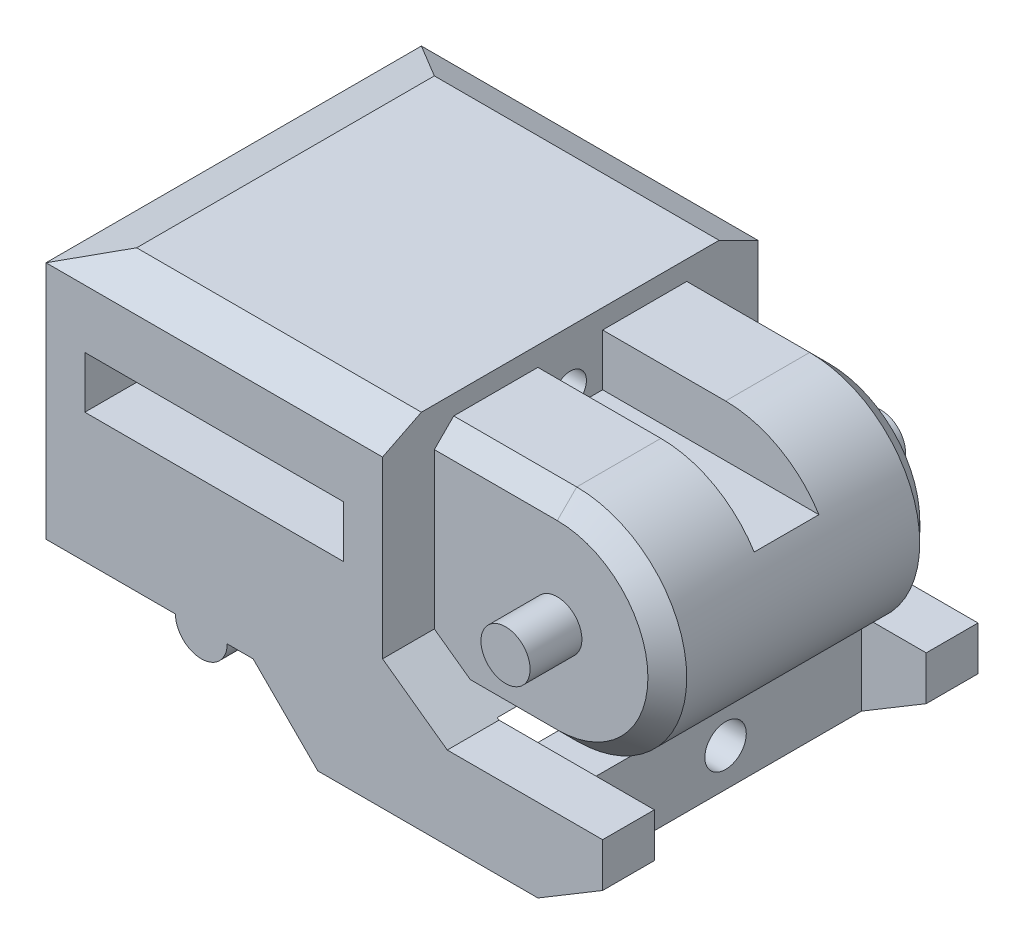
SolidWorks part; units mm, degrees
ref_plane "Front Plane" through (0, 0, 0) normal (0, 0, 1) x (1, 0, 0)
ref_plane "Top Plane" through (0, 0, 0) normal (0, 1, 0) x (1, 0, 0)
ref_plane "Right Plane" through (0, 0, 0) normal (1, 0, 0) x (0, 0, -1)
sketch "Sketch1" plane through (0, 0, 0) normal (0, 1, 0) x (1, 0, 0)
  line L0 (-8.5, 14.5) -> (-8.5, -14.5)
  line L1 (-8.5, -14.5) -> (35.5, -14.5)
  line L3 (-8.5, 14.5) -> (35.5, 14.5)
  line L4 (35.5, -14.5) -> (35.5, 14.5)
  line L5 (-8.5, -3.4718) -> (35.5, 14.5) construction
  line L7 (17.5, 14.5) -> (17.5, -14.5)
  line L10 (17.5, 10.5) -> (35.5, 10.5)
  line L11 (17.5, -10.5) -> (35.5, -10.5)
  line L12 (-8.5, 5.5141) -> (35.5, -14.5) construction
  point P0 (0, 0)
  dimension "D1" = 29
  dimension "D2" = 44
  dimension "D4" = 18
  dimension "D7" = 4
  dimension "D8" = 4
extrude "Boss-Extrude1" add sketch "Sketch1" along normal blind 20 contours L7 L3 L0 L1 | L7 L11 L4 L10
sketch "Sketch3" plane through (0, 0, 14.5) normal (0, 0, 1) x (1, 0, 0)
  line L0 (-8.5, 20) -> (-8.5, 18.5)
  line L1 (-8.5, 20) -> (-8.5, 0) construction
  line L2 (-8.5, 18.5) -> (-4.5, 20)
  line L3 (-4.5, 20) -> (-8.5, 20)
  dimension "D1" = 1.5
  dimension "D2" = 4
extrude "Cut-Extrude3" cut sketch "Sketch3" against normal through all
sketch "Sketch4" plane through (17.5, 0, 0) normal (1, 0, 0) x (0, 0, -1)
  line L0 (-14.5, 20) -> (-14.5, 18.5)
  line L1 (-14.5, 20) -> (-14.5, 0) construction
  line L2 (-14.5, 18.5) -> (-11.5, 20)
  line L3 (14.5, 20) -> (10.5, 20) construction
  line L4 (-11.5, 20) -> (-14.5, 20)
  line L5 (14.5, 20) -> (11.5, 20)
  line L6 (11.5, 20) -> (14.5, 18.5)
  line L7 (14.5, 20) -> (14.5, 0) construction
  line L8 (14.5, 18.5) -> (14.5, 20)
  dimension "D1" = 3
  dimension "D2" = 1.5
  dimension "D3" = 1.5
  dimension "D4" = 3
extrude "Cut-Extrude4" cut sketch "Sketch4" against normal through all
sketch "Sketch6" plane through (0, 0, 0) normal (0, -1, 0) x (1, 0, 0)
  line L0 (-8.5, -14.5) -> (17.5, -14.5) construction
  line L1 (-5.5, 8.5) -> (14.5, 8.5)
  line L2 (-5.5, 8.5) -> (-5.5, -8.5)
  line L3 (-5.5, -8.5) -> (14.5, -8.5)
  line L4 (14.5, 8.5) -> (14.5, -8.5)
  line L5 (-8.5, -14.5) -> (-8.5, 14.5) construction
  line L6 (-8.5, 14.5) -> (17.5, 14.5) construction
  line L7 (17.5, -14.5) -> (17.5, -10.5) construction
  dimension "D1" = 6
  dimension "D2" = 3
  dimension "D3" = 6
  dimension "D4" = 3
extrude "Cut-Extrude5" cut sketch "Sketch6" against normal blind 17
sketch "Sketch9" plane through (-8.5, 0, 0) normal (-1, 0, 0) x (0, 0, 1)
  line L0 (-14.5, 18.5) -> (-14.5, 0) construction
  line L1 (-8.5, 17) -> (8.5, 17)
  line L2 (-8.5, 17) -> (-8.5, 13)
  line L3 (-8.5, 13) -> (8.5, 13)
  line L4 (8.5, 17) -> (8.5, 13)
  line L5 (14.5, 18.5) -> (14.5, 0) construction
  line L6 (-14.5, 18.5) -> (14.5, 18.5) construction
  dimension "D1" = 6
  dimension "D2" = 6
  dimension "D3" = 1.5
  dimension "D4" = 4
extrude "Cut-Extrude7" cut sketch "Sketch9" against normal blind 4
sketch "Sketch10" plane through (0, 0, 14.5) normal (0, 0, 1) x (1, 0, 0)
  line L0 (-8.5, 18.5) -> (-8.5, 0) construction
  line L1 (-5.5, 14) -> (14.5, 14)
  line L2 (-5.5, 14) -> (-5.5, 10)
  line L3 (-5.5, 10) -> (14.5, 10)
  line L4 (14.5, 14) -> (14.5, 10)
  line L5 (17.5, 18.5) -> (17.5, 0) construction
  line L6 (-4.5, 20) -> (17.5, 20) construction
  dimension "D1" = 3
  dimension "D2" = 3
  dimension "D3" = 4
  dimension "D4" = 6
extrude "Cut-Extrude8" cut sketch "Sketch10" against normal through all
sketch "Sketch12" plane through (0, 0, 14.5) normal (0, 0, 1) x (1, 0, 0)
  line L0 (22.5, 1.4) -> (34.5, 1.4)
  line L4 (17.5, 20) -> (17.5, 0) construction
  line L5 (17.5, 5) -> (22.5, 1.4)
  line L6 (17.5, 5) -> (17.5, 0)
  line L7 (17.5, 0) -> (7.5, 0)
  line L8 (-8.5, 0) -> (17.5, 0) construction
  line L9 (7.5, 0) -> (12.5, -5)
  line L10 (12.5, -5) -> (29.5, -5)
  line L12 (34.5, 0) -> (34.5, 1.4)
  line L14 (34.5, 0) -> (34.5, -2)
  line L15 (34.5, -2) -> (29.5, -5)
  line L16 (17.5, 0) -> (35.5, 0) construction
  dimension "D1" = 10
  dimension "D2" = 17
  dimension "D3" = 5
  dimension "D4" = 5
  dimension "D5" = 5
  dimension "D6" = 5
  dimension "D7" = 2
  dimension "D8" = 1.4
  dimension "D9" = 5
extrude "Boss-Extrude3" add sketch "Sketch12" against normal blind 4
mirror "Mirror1" about plane through (0, 0, 0) normal (0, 0, 1) of "Boss-Extrude3"
sketch "Sketch13" plane through (0, 0, 10.5) normal (0, 0, 1) x (1, 0, 0)
  line L0 (35.5, 20) -> (35.5, 0) construction
  line L1 (17.5, 20) -> (35.5, 20)
  line L2 (17.5, 20) -> (17.5, 18.5)
  line L3 (17.5, 18.5) -> (35.5, 18.5)
  line L4 (35.5, 20) -> (35.5, 18.5)
  line L11 (35.5, 0) -> (15.5, 0)
  line L12 (35.5, 0) -> (35.5, 1.5)
  line L13 (35.5, 1.5) -> (15.5, 1.5)
  line L14 (15.5, 0) -> (15.5, 1.5)
  dimension "D1" = 1.5
  dimension "D2" = 1.5
  dimension "D3" = 20
extrude "Cut-Extrude11" cut sketch "Sketch13" against normal blind 21
sketch "Sketch14" plane through (0, 0, 10.5) normal (0, 0, 1) x (1, 0, 0)
  line L0 (35.5, 1.5) -> (22.3611, 1.5) construction
  line L1 (35.5, 18.5) -> (35.5, 1.5) construction
  line L3 (27, 18.5) -> (35.5, 18.5)
  line L4 (27, 18.5) -> (27, 1.5)
  line L5 (27, 1.5) -> (35.5, 1.5)
  line L6 (35.5, 18.5) -> (35.5, 1.5)
  circle A0 centre (27, 10) radius 8.5
  line M1 (35.5, 1.5) -> (35.5, 18.5)
  line M2 (35.5, 18.5) -> (17.5, 18.5)
  line M5 (22.3611, 1.5) -> (35.5, 1.5)
  dimension "D3" = 17
  dimension "D1" = 8.5
  dimension "D2" = 8.5
extrude "Cut-Extrude12" cut sketch "Sketch14" against normal through all contours A0 M5 M1 | A0 L6 M2
ref_plane "Plane1" through (0, 0, 0) normal (0, 0, 1) x (1, 0, 0)
sketch "Sketch16" plane through (0, 0, 0) normal (0, 0, 1) x (1, 0, 0)
  circle A0 centre (27, 10) radius 1.9
  dimension "D1" = 3.8
extrude "Boss-Extrude4" add sketch "Sketch16" along normal mid plane 29
sketch "Sketch22" plane through (17.5, 0, 0) normal (1, 0, 0) x (0, 0, -1)
  line L0 (11.5, 20) -> (-11.5, 20) construction
  line L1 (-14.5, 18.5) -> (-14.5, 5) construction
  circle A0 centre (0, 15.75) radius 1.25
  dimension "D1" = 2.5
  dimension "D2" = 4.25
  dimension "D3" = 14.5
extrude "Cut-Extrude15" cut sketch "Sketch22" against normal through all both and the other way through all
chamfer "Chamfer1" distance 1.5 angle 45 6 edges at (24.6806, 1.5, 10.5) (22.25, 18.5, 10.5) (35.5, 10, 10.5) (22.25, 18.5, -10.5) (24.6806, 1.5, -10.5) (35.5, 10, -10.5)
sketch "Sketch23" plane through (0, 18.5, 0) normal (0, 1, 0) x (1, 0, 0)
  line L0 (17.5, 11.5) -> (17.5, -11.5) construction
  line L1 (17.5, 2.5) -> (35.5, 2.5)
  line L2 (17.5, 2.5) -> (17.5, -2.5)
  line L3 (17.5, -2.5) -> (35.5, -2.5)
  line L4 (35.5, 2.5) -> (35.5, -2.5)
  line L5 (35.5, -9) -> (35.5, 9) construction
  line L6 (27, 9) -> (17.5, 9) construction
  line L7 (17.5, -9) -> (27, -9) construction
  dimension "D1" = 6.5
  dimension "D2" = 6.5
extrude "Cut-Extrude16" cut sketch "Sketch23" against normal blind 4
sketch "Sketch24" plane through (0, 0, 14.5) normal (0, 0, 1) x (1, 0, 0)
  line L0 (-8.5, 0) -> (7.5, 0) construction
  circle A0 centre (3.5, 0) radius 2
  dimension "D1" = 4
  dimension "D2" = 3.5
extrude "Boss-Extrude7" add sketch "Sketch24" against normal through all
sketch "Sketch25" plane through (0, 0, 14.5) normal (0, 0, 1) x (1, 0, 0)
  line L0 (34.5, 1.4) -> (22.5, 1.4) construction
  line L1 (29.5, -5) -> (25, -5)
  line L2 (29.5, -5) -> (29.5, 0.9)
  line L3 (29.5, 0.9) -> (25, 0.9)
  line L4 (25, -5) -> (25, 0.9)
  dimension "D1" = 4.5
  dimension "D2" = 0.5
extrude "Boss-Extrude8" add sketch "Sketch25" against normal through all
sketch "Sketch26" plane through (29.5, 0, 0) normal (1, 0, 0) x (0, 0, -1)
  line L0 (10.5, 0.9) -> (-10.5, 0.9) construction
  circle A0 centre (0, -2.05) radius 1.6
  dimension "D1" = 3.2
  dimension "D2" = 2.95
extrude "Cut-Extrude17" cut sketch "Sketch26" against normal blind 10
